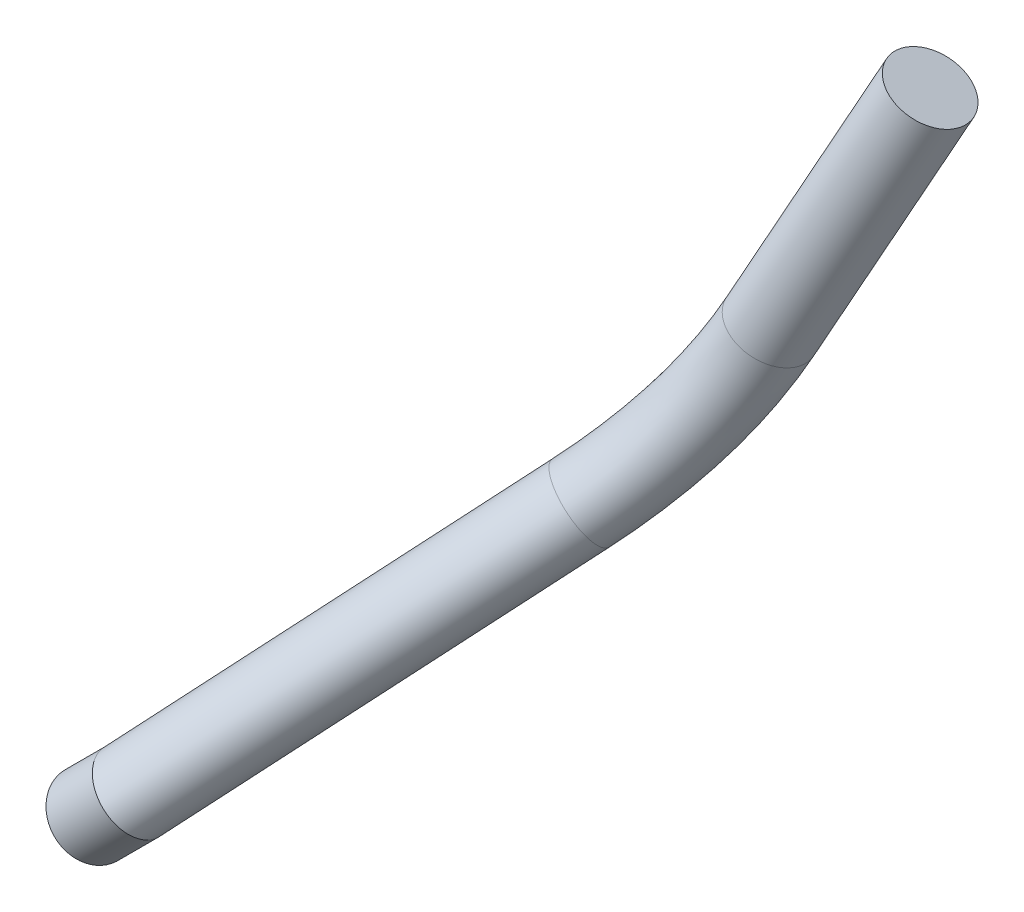
SolidWorks part; units mm, degrees
ref_plane "X-Y Datum" through (0, 0, 0) normal (0, 0, 1) x (1, 0, 0)
ref_plane "X-Z Datum" through (0, 0, 0) normal (0, 1, 0) x (1, 0, 0)
ref_plane "Y-Z Datum" through (0, 0, 0) normal (1, 0, 0) x (0, 0, -1)
sketch3d "3DSketch1"
  line L0 (238.7544, 134.2697, 168.7024) -> (253.6203, 165.14, 163.3218)
  line L1 (198.0851, 82.9911, 208.7608) -> (193.0109, 77.9169, 208.7608)
  line L2 (198.0851, 82.9911, 208.7608) -> (225.2152, 113.3685, 179.1128)
  circle A0 centre (198.0851, 82.9911, 208.7608) radius 2.5146 construction
  arc A1 (253.6579, 165.1264, 159.3218) -> (253.6579, 165.1264, 167.3218) centre (253.6579, 165.1264, 163.3218) ccw construction
  arc A2 (253.6203, 165.14, 168.0218) -> (253.6203, 165.14, 158.6218) centre (253.6203, 165.14, 163.3218) ccw construction
  arc A3 (225.2152, 113.3685, 179.1128) -> (238.7544, 134.2697, 168.7024) centre (221.8528, 150.2787, 213.8543) ccw
  point P0 (198.0851, 82.9911, 208.7608)
  point P1 (253.6579, 165.1264, 163.3218)
  point P4 (199.8733, 84.7591, 208.7608)
  point P9 (252.2924, 161.3666, 163.3218)
  point P17 (252.0158, 160.7224, 163.3218)
  point P18 (232.7542, 121.8098, 170.8742)
  point P19 (264.5246, 133.5478, 235.7596)
  dimension "D1" = 50.8
sweep "Sweep1" add path "3DSketch1" circular profile diameter 9.398 parameters "D3"=9.398
